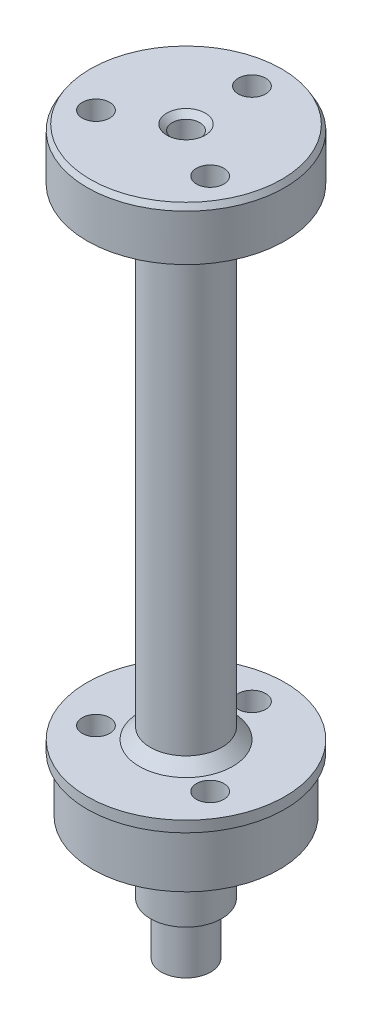
SolidWorks part; units mm, degrees
material "6061 合金"
ref_plane "前视基准面" through (0, 0, 0) normal (0, 0, 1) x (1, 0, 0)
ref_plane "上视基准面" through (0, 0, 0) normal (0, 1, 0) x (1, 0, 0)
ref_plane "右视基准面" through (0, 0, 0) normal (1, 0, 0) x (0, 0, -1)
sketch "草图2" plane through (0, 0, 0) normal (0, 0, 1) x (1, 0, 0)
  line L0 (0, 60) -> (0, 0) construction
  line L1 (3.25, 0) -> (8.5, 0)
  line L4 (9, 5) -> (9, 6)
  line L5 (9, 54.5) -> (1.25, 54.5)
  line L6 (1.25, 54.5) -> (1.25, -11.5)
  line L8 (8.5, 5) -> (8.5, 0)
  line L9 (9, 49.5) -> (9, 54.5)
  line L12 (8.5, 5) -> (9, 5)
  line L13 (9, 49.5) -> (3.25, 49.5)
  line L15 (9, 6) -> (3.25, 6)
  line L16 (3.25, 49.5) -> (3.25, 6)
  line L17 (2.25, -6.5) -> (2.25, -11.5)
  line L18 (2.25, -11.5) -> (1.25, -11.5)
  line L21 (3.25, 0) -> (3.25, -6.5)
  line L22 (3.25, -6.5) -> (2.25, -6.5)
  dimension "D1" = 17
  dimension "D2" = 5
  dimension "D3" = 54.5
  dimension "D4" = 18
  dimension "D5" = 5
  dimension "D6" = 1
  dimension "D7" = 2.5
  dimension "D8" = 1
  dimension "D9" = 6.5
  dimension "D10" = 1
  dimension "D11" = 5
revolve "旋转1" add sketch "草图2" angle 360 about L0
hole_wizard "M3 螺纹孔1" positions "草图13" profile "草图14" tap size "M3" standard "GB" end condition through all
sketch "草图13" plane through (0, 54.5, 0) normal (0, 1, 0) x (1, 0, 0)
  circle A0 centre (0, 0) radius 6 construction
  circle A2 centre (0, 0) radius 8.5 construction
  point P9 (0, 6)
  point P15 (5.1962, -3)
  point P16 (-5.1962, -3)
  dimension "D1" = 2.5
  dimension "D2" = 3
cosmetic thread "孔螺蚊线1" parameters "D2"=3
cosmetic thread "孔螺蚊线2" parameters "D2"=3
cosmetic thread "孔螺蚊线3" parameters "D2"=3
sketch "草图14" plane through (-5.1962, 54.5, 3) normal (1, 0, 0) x (0, 0, 1)
  line L0 (0, 0) -> (0, 66)
  line L1 (0, 66) -> (1.25, 66)
  line L2 (1.25, 66) -> (1.25, 0)
  line L5 (1.25, 0) -> (0, 0)
  line L11 (0, -6.35) -> (0, 107.95) construction
  dimension "通孔螺纹孔钻头直径" = 2.5
  dimension "通孔螺纹孔钻头深度" = 66
chamfer "倒角1" distance 1 angle 45 2 edges at (0, 6, 3.25) (0, 49.5, 3.25)
chamfer "倒角2" distance 0.5 angle 30 3 edges at (0, -11.5, 2.25) (0, 49.5, 9) (0, 54.5, 9)
hole_wizard "M3 螺纹孔2" positions "草图15" profile "草图16" tap size "M3" standard "GB"
sketch "草图15" plane through (0, 54.5, 0) normal (0, 1, 0) x (1, 0, 0)
  point P0 (0, 0)
sketch "草图16" plane through (0, 54.5, 0) normal (1, 0, 0) x (0, 0, 1)
  line L0 (0, 0) -> (0, 6.7511)
  line L1 (0, 6.7511) -> (1.25, 6)
  line L2 (1.25, 6) -> (1.25, 0.5)
  line L3 (1.25, 0.5) -> (1.75, 0)
  line L5 (1.75, 0) -> (0, 0)
  line L6 (-1.25, 0.5) -> (-1.75, 0) construction
  line L10 (0, 6.7511) -> (-1.25, 6) construction
  line L11 (0, -6.35) -> (0, 107.95) construction
  dimension "螺纹孔钻头直径" = 2.5
  dimension "螺纹孔钻头深度" = 6
  dimension "近端锥形沉头孔直径" = 3.5
  dimension "近端锥形沉头孔角度" = 90
  dimension "导头角度" = 118
cosmetic thread "孔螺蚊线5" parameters "D1"=6, "D2"=3
